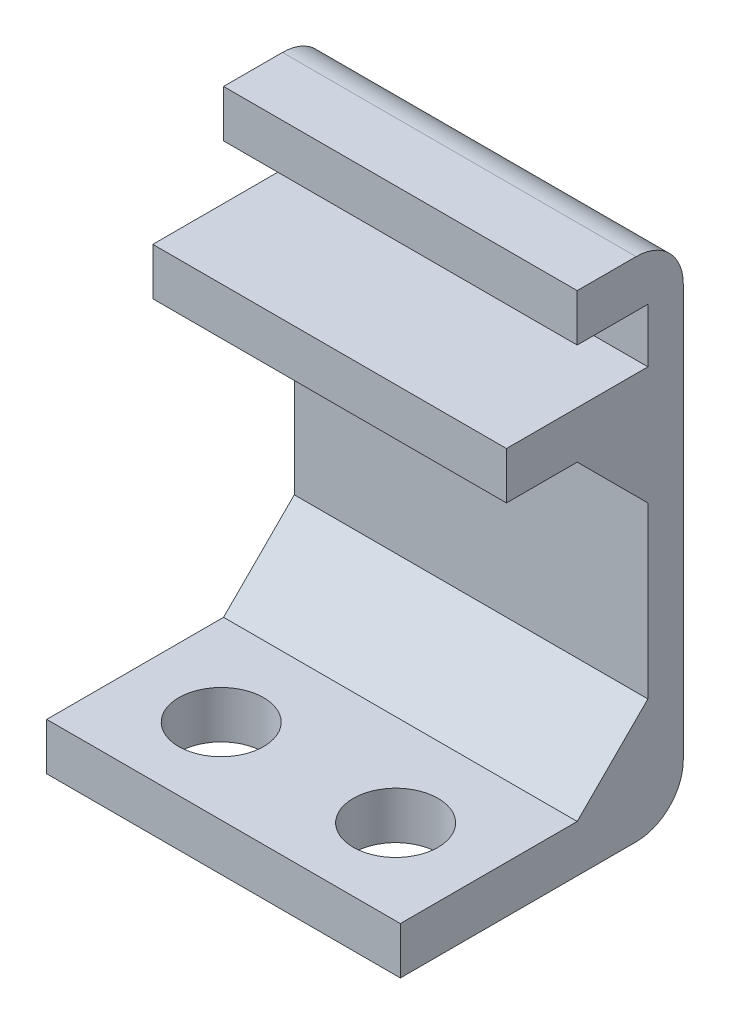
SolidWorks part; units mm, degrees
ref_plane "Plano frontal" through (0, 0, 0) normal (0, 0, 1) x (1, 0, 0)
ref_plane "Plano superior" through (0, 0, 0) normal (0, 1, 0) x (1, 0, 0)
ref_plane "Plano direito" through (0, 0, 0) normal (1, 0, 0) x (0, 0, -1)
sketch "Sketch1" plane through (0, 0, 0) normal (1, 0, 0) x (0, 0, -1)
  line L0 (-5.25, -8.75) -> (-5.25, -10.75)
  line L1 (2.25, 10.75) -> (6.75, 10.75)
  line L2 (2.25, 10.75) -> (2.25, 8.75)
  line L3 (-5.25, -10.75) -> (6.75, -10.75)
  line L4 (6.75, 10.75) -> (6.75, -10.75)
  line L5 (2.25, 8.75) -> (5.25, 8.75)
  line L7 (-5.25, -8.75) -> (5.25, -8.75)
  line L8 (5.25, 8.75) -> (5.25, 6.45)
  line L9 (5.25, 4.45) -> (5.25, -8.75)
  line L10 (-0.75, 6.45) -> (5.25, 6.45)
  line L11 (-0.75, 6.45) -> (-0.75, 4.45)
  line L12 (-0.75, 4.45) -> (5.25, 4.45)
  point P7 (6.75, 0)
  point P15 (0, -8.75)
  dimension "D1" = 17.2
  dimension "D2" = 12
  dimension "D3" = 1.5
  dimension "D4" = 2
  dimension "D5" = 2.3
  dimension "D6" = 4.5
  dimension "D7" = 6
extrude "Boss-Extrude1" add sketch "Sketch1" along normal mid plane 15 contours L5 L8 L7 L2 L3 L4 L1
chamfer "Chamfer1" distance 3 angle 45 2 edges at (0, 4.45, -5.25) (0, -8.75, -5.25)
sketch "Sketch2" plane through (0, -8.75, 0) normal (0, 1, 0) x (1, 0, 0)
  line L1 (-7.5, -5.25) -> (-7.5, 2.25) construction
  line L2 (0, -55) -> (0, 55) construction
  line L3 (7.5, -5.25) -> (-7.5, -5.25) construction
  circle A0 centre (-3.7, -1.65) radius 1.5 construction
  circle A1 centre (-3.7, -1.65) radius 1.8
  circle A2 centre (3.7, -1.65) radius 1.5 construction
  circle A3 centre (3.7, -1.65) radius 1.8
  dimension "D1" = 3
  dimension "D3" = 2
  dimension "D4" = 1.8
  dimension "D2" = 0.3
extrude "Cut-Extrude1" cut sketch "Sketch2" against normal through all and the other way blind 3
fillet "Fillet1" radius 2 2 edges at (0, -10.75, -6.75) (0, 10.75, -6.75)
